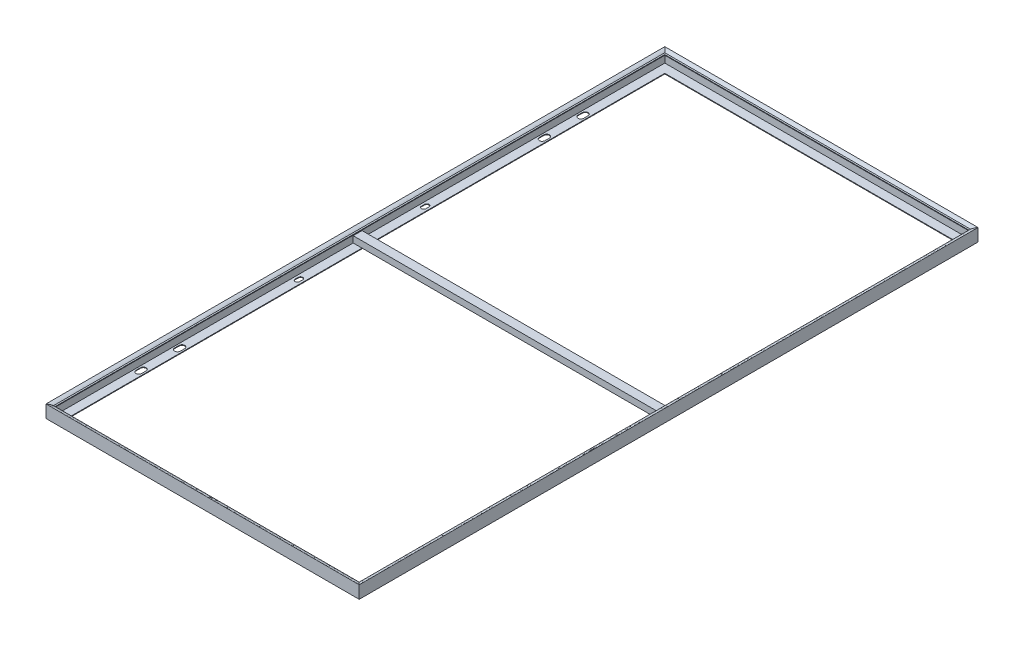
SolidWorks part; units mm, degrees
material "6063-T6"
ref_plane "Front Plane" through (0, 0, 0) normal (0, 0, 1) x (1, 0, 0)
ref_plane "Top Plane" through (0, 0, 0) normal (0, 1, 0) x (1, 0, 0)
ref_plane "Right Plane" through (0, 0, 0) normal (1, 0, 0) x (0, 0, -1)
sketch "Sketch1" plane through (0, 0, 0) normal (0, 1, 0) x (1, 0, 0)
  line L1 (-496, 980) -> (496, 980)
  line L2 (-496, 980) -> (-496, -980)
  line L3 (-496, -980) -> (496, -980)
  line L4 (496, 980) -> (496, -980)
  line L5 (-496, 980) -> (496, -980) construction
  line L6 (-496, -980) -> (496, 980) construction
  point P0 (0, 0)
  dimension "D1" = 992
  dimension "D2" = 1960
sketch "Sketch2" plane through (0, 0, 0) normal (0, 0, 1) x (1, 0, 0)
  line L11 (-496, 0) -> (496, 0) construction
  line L12 (481.3859, 15) -> (488.6141, 15) construction
  line L22 (491, -18) -> (494, 8.5) construction
  line L23 (491, 8.5) -> (494, -18) construction
  line L24 (494, 8.5) -> (494, -18)
  line L25 (491, -18) -> (494, -18)
  line L26 (491, 8.5) -> (491, -18)
  line L27 (491, 8.5) -> (494, 8.5)
  line L28 (461, -18) -> (461, -20)
  line L29 (489, -18) -> (461, -18)
  line L30 (489, 8.5) -> (489, -18)
  line L31 (484, 8.5) -> (489, 8.5)
  line L32 (484, 10.5) -> (484, 8.5)
  line L33 (494, 10.5) -> (484, 10.5)
  line L34 (494, 15) -> (494, 10.5)
  line L35 (485, 15) -> (494, 15)
  line L36 (496, -20) -> (496, 20)
  line L37 (461, -20) -> (496, -20)
  spline S0 degree 3 poles (485, 15) (480.4824, 15) (496.0054, 21.4267) (496, 20) knots 0 0 0 0 1 1 1 1
  point P1 (496, 0)
  dimension "D1" = 2
  dimension "D2" = 35
  dimension "D3" = 40
  dimension "D4" = 4.5
  dimension "D5" = 26.5
  dimension "D6" = 2
  dimension "D7" = 2
  dimension "D8" = 11
  dimension "D9" = 10
  dimension "D10" = 2
  dimension "D11" = 2
  dimension "D12" = 28
  dimension "D13" = 496
sweep "Sweep1" add profiles "Sketch2" path "Sketch1"
sketch "Sketch3" plane through (-489, 0, 0) normal (1, 0, 0) x (0, 0, -1)
  line L1 (-14, 2) -> (14, 2)
  line L2 (-14, 2) -> (-14, -18)
  line L3 (-14, -18) -> (14, -18)
  line L4 (14, 2) -> (14, -18)
  line L5 (-14, 2) -> (14, -18) construction
  line L6 (-14, -18) -> (14, 2) construction
  line L8 (-973, -18) -> (973, -18) construction
  line L9 (12, 0) -> (12, -16)
  line L10 (-12, -16) -> (12, -16)
  line L11 (-12, 0) -> (-12, -16)
  line L12 (-12, 0) -> (12, 0)
  point P0 (0, -8)
  point P6 (0, 0)
  point P8 (10.8578, 11.6693)
  point P10 (0, 0)
  point P11 (0, -18)
  point P12 (0, -18)
  dimension "D1" = 28
  dimension "D2" = 20
  dimension "D3" = 2
extrude "Boss-Extrude1" add sketch "Sketch3" along normal up to surface (978 mm away) up to face at (489, -4.75, 0)
sketch "Sketch4" plane through (0, -20, 0) normal (0, -1, 0) x (1, 0, 0)
  line L0 (0, -945) -> (0, 945) construction
  line L1 (-461, -945) -> (461, -945) construction
  line L2 (461, 945) -> (-461, 945) construction
  line L3 (-461, 0) -> (461, 0) construction
  line L4 (-461, 14) -> (-461, -14) construction
  line L5 (461, 14) -> (461, -14) construction
  line L6 (475, 205) -> (475, 195) construction
  line L7 (482, 205) -> (482, 195)
  line L8 (468, 205) -> (468, 195)
  line L9 (496, -980) -> (496, 980) construction
  line L11 (475, 584.5) -> (475, 570.5) construction
  line L12 (484, 584.5) -> (484, 570.5)
  line L13 (466, 584.5) -> (466, 570.5)
  line L14 (475, 707) -> (475, 693) construction
  line L15 (484, 707) -> (484, 693)
  line L16 (466, 707) -> (466, 693)
  line L17 (-475, 707) -> (-475, 693) construction
  line L18 (-484, 707) -> (-484, 693)
  line L19 (-466, 707) -> (-466, 693)
  line L20 (-475, 584.5) -> (-475, 570.5) construction
  line L21 (-484, 584.5) -> (-484, 570.5)
  line L22 (-466, 584.5) -> (-466, 570.5)
  line L23 (-475, 205) -> (-475, 195) construction
  line L24 (-482, 205) -> (-482, 195)
  line L25 (-468, 205) -> (-468, 195)
  line L26 (-475, -205) -> (-475, -195) construction
  line L27 (-482, -205) -> (-482, -195)
  line L28 (-468, -205) -> (-468, -195)
  line L29 (-475, -584.5) -> (-475, -570.5) construction
  line L30 (-484, -584.5) -> (-484, -570.5)
  line L31 (-466, -584.5) -> (-466, -570.5)
  line L32 (-475, -707) -> (-475, -693) construction
  line L33 (-484, -707) -> (-484, -693)
  line L34 (-466, -707) -> (-466, -693)
  line L35 (475, -707) -> (475, -693) construction
  line L36 (484, -707) -> (484, -693)
  line L37 (466, -707) -> (466, -693)
  line L38 (475, -584.5) -> (475, -570.5) construction
  line L39 (484, -584.5) -> (484, -570.5)
  line L40 (466, -584.5) -> (466, -570.5)
  line L41 (475, -205) -> (475, -195) construction
  line L42 (482, -205) -> (482, -195)
  line L43 (468, -205) -> (468, -195)
  arc A0 (482, 205) -> (468, 205) centre (475, 205) ccw
  arc A1 (468, 195) -> (482, 195) centre (475, 195) ccw
  arc A2 (484, 584.5) -> (466, 584.5) centre (475, 584.5) ccw
  arc A3 (466, 570.5) -> (484, 570.5) centre (475, 570.5) ccw
  arc A4 (484, 707) -> (466, 707) centre (475, 707) ccw
  arc A5 (466, 693) -> (484, 693) centre (475, 693) ccw
  arc A6 (-484, 707) -> (-466, 707) centre (-475, 707) cw
  arc A7 (-466, 693) -> (-484, 693) centre (-475, 693) cw
  arc A8 (-484, 584.5) -> (-466, 584.5) centre (-475, 584.5) cw
  arc A9 (-466, 570.5) -> (-484, 570.5) centre (-475, 570.5) cw
  arc A10 (-482, 205) -> (-468, 205) centre (-475, 205) cw
  arc A11 (-468, 195) -> (-482, 195) centre (-475, 195) cw
  arc A12 (-482, -205) -> (-468, -205) centre (-475, -205) ccw
  arc A13 (-468, -195) -> (-482, -195) centre (-475, -195) ccw
  arc A14 (-484, -584.5) -> (-466, -584.5) centre (-475, -584.5) ccw
  arc A15 (-466, -570.5) -> (-484, -570.5) centre (-475, -570.5) ccw
  arc A16 (-484, -707) -> (-466, -707) centre (-475, -707) ccw
  arc A17 (-466, -693) -> (-484, -693) centre (-475, -693) ccw
  arc A18 (484, -707) -> (466, -707) centre (475, -707) cw
  arc A19 (466, -693) -> (484, -693) centre (475, -693) cw
  arc A20 (484, -584.5) -> (466, -584.5) centre (475, -584.5) cw
  arc A21 (466, -570.5) -> (484, -570.5) centre (475, -570.5) cw
  arc A22 (482, -205) -> (468, -205) centre (475, -205) cw
  arc A23 (468, -195) -> (482, -195) centre (475, -195) cw
  point P14 (475, 200)
  point P19 (479.2519, 200)
  point P24 (475, 577.5)
  point P29 (475, 276.1252)
  point P30 (471.6754, 265.5634)
  point P31 (0, 0)
  point P32 (475, 597.5027)
  point P33 (0, 0)
  point P36 (475, 700)
  point P41 (0, 0)
  point P44 (-475, 700)
  point P51 (-475, 577.5)
  point P58 (-475, 200)
  point P65 (-475, -200)
  point P72 (-475, -577.5)
  point P79 (-475, -700)
  point P86 (475, -700)
  point P93 (475, -577.5)
  point P100 (475, -200)
  dimension "D2" = 7
  dimension "D5" = 9
  dimension "D8" = 9
  dimension "D1" = 10
  dimension "D3" = 200
  dimension "D4" = 21
  dimension "D6" = 14
  dimension "D7" = 577.5
  dimension "D9" = 14
  dimension "D10" = 700
extrude "Cut-Extrude1" cut sketch "Sketch4" against normal up to surface (2 mm away) up to face at (0, -18, -486.5)
